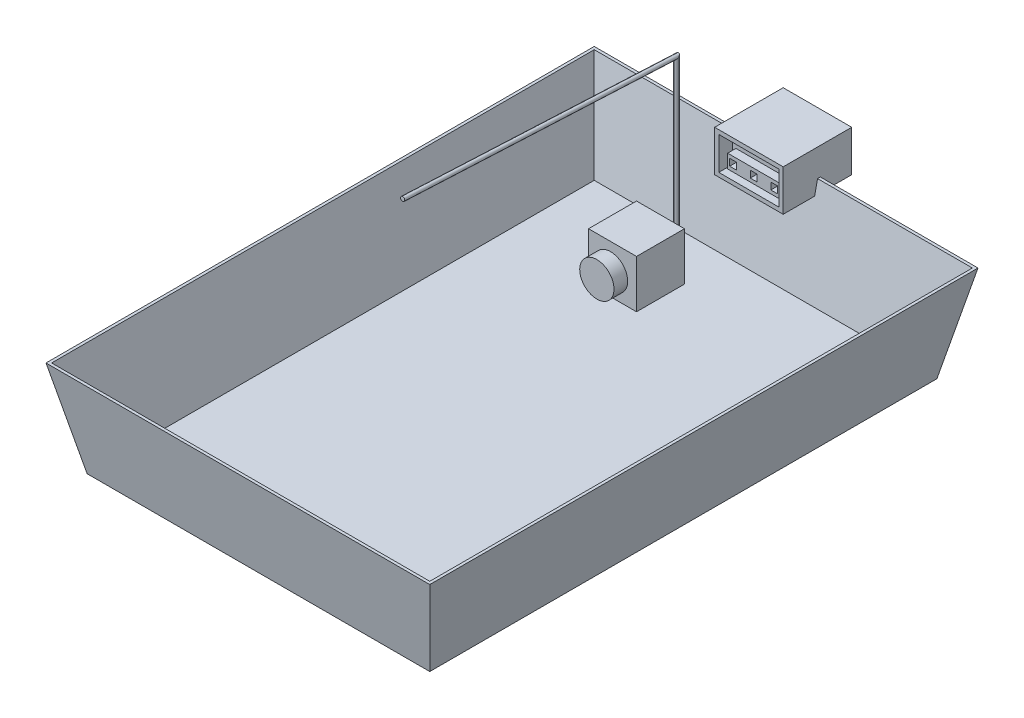
SolidWorks part; units mm, degrees
ref_plane "Front Plane" through (0, 0, 0) normal (0, 0, 1) x (1, 0, 0)
ref_plane "Top Plane" through (0, 0, 0) normal (0, 1, 0) x (1, 0, 0)
ref_plane "Right Plane" through (0, 0, 0) normal (1, 0, 0) x (0, 0, -1)
sketch "Sketch1" plane through (0, 0, 0) normal (0, 1, 0) x (1, 0, 0)
  line L1 (-140, 200) -> (140, 200)
  line L2 (-140, 200) -> (-140, -200)
  line L3 (-140, -200) -> (140, -200)
  line L4 (140, 200) -> (140, -200)
  line L5 (-140, 200) -> (140, -200) construction
  line L6 (-140, -200) -> (140, 200) construction
  point P0 (0, 0)
  dimension "D1" = 400
  dimension "D2" = 280
ref_plane "Plane1" through (0, -70, 0) normal (0, 1, 0) x (1, 0, 0)
sketch "Sketch2" plane through (0, -70, 0) normal (0, 1, 0) x (1, 0, 0)
  line L8 (125, 185) -> (-125, 185)
  line L9 (125, -185) -> (125, 185)
  line L10 (-125, -185) -> (125, -185)
  line L11 (-125, 185) -> (-125, -185)
  line L12 (125, 185) -> (-125, 185)
  line L13 (125, -185) -> (125, 185)
  line L14 (-125, -185) -> (125, -185)
  line L15 (-125, 185) -> (-125, -185)
  dimension "D1" = 15
loft "Loft1" add profiles "Sketch2", "Sketch1"
shell "Shell1" thickness 2
sketch "Sketch3" plane through (0, 0, 0) normal (0, 1, 0) x (1, 0, 0)
  line L0 (140, 200) -> (-140, 200) construction
  line L1 (-25, 225) -> (25, 225)
  line L2 (-25, 225) -> (-25, 175)
  line L3 (-25, 175) -> (25, 175)
  line L4 (25, 225) -> (25, 175)
  line L5 (-25, 225) -> (25, 175) construction
  line L6 (-25, 175) -> (25, 225) construction
  point P0 (0, 200)
  dimension "D1" = 50
extrude "Cut-Extrude1" cut sketch "Sketch3" against normal blind 10
sketch "Sketch4" plane through (0, -10, 0) normal (0, 1, 0) x (1, 0, 0)
  line L0 (25, 197.8571) -> (-25, 197.8571) construction
  line L1 (25, 172.8571) -> (-25, 172.8571)
  line L2 (25, 172.8571) -> (25, 222.8571)
  line L3 (25, 222.8571) -> (-25, 222.8571)
  line L4 (-25, 172.8571) -> (-25, 222.8571)
  line L5 (25, 172.8571) -> (-25, 222.8571) construction
  line L6 (25, 222.8571) -> (-25, 172.8571) construction
  point P0 (0, 197.8571)
  dimension "D1" = 50
extrude "Boss-Extrude2" add sketch "Sketch4" along normal blind 30 separate body
sketch "Sketch6" plane through (0, 0, -172.8571) normal (0, 0, 1) x (1, 0, 0)
  line L14 (-22, -7) -> (22, -7)
  line L15 (22, -7) -> (22, 17)
  line L16 (-22, 17) -> (-22, -7)
  line L17 (22, 17) -> (-22, 17)
  line L18 (-22, -7) -> (22, -7)
  line L19 (22, -7) -> (22, 17)
  line L20 (-22, 17) -> (-22, -7)
  line L21 (22, 17) -> (-22, 17)
  dimension "D1" = 3
extrude "Cut-Extrude2" cut sketch "Sketch6" against normal blind 10
sketch "Sketch7" plane through (0, 0, -222.8571) normal (0, 0, -1) x (-1, 0, 0)
  line L8 (-20, -5) -> (20, -5)
  line L9 (20, -5) -> (20, 15)
  line L10 (20, 15) -> (-20, 15)
  line L11 (-20, 15) -> (-20, -5)
  line L12 (-20, -5) -> (20, -5)
  line L13 (20, -5) -> (20, 15)
  line L14 (20, 15) -> (-20, 15)
  line L15 (-20, 15) -> (-20, -5)
  dimension "D1" = 5
extrude "Cut-Extrude3" cut sketch "Sketch7" against normal blind 10
sketch "Sketch8" plane through (0, 0, -182.8571) normal (0, 0, 1) x (1, 0, 0)
  circle A0 centre (-15.3016, 11.712) radius 2.5
  circle A1 centre (-7.1335, 11.712) radius 2.5
  dimension "D1" = 5
  dimension "D2" = 5
extrude "Cut-Extrude4" cut sketch "Sketch8" against normal blind 60
sketch "Sketch9" plane through (0, 0, -182.8571) normal (0, 0, 1) x (1, 0, 0)
  line L0 (-19.4953, 4.3816) -> (20.5047, 4.3816)
  line L1 (20.5047, 4.3816) -> (20.5047, -5.6184)
  line L2 (20.5047, -5.6184) -> (-19.4953, -5.6184)
  line L3 (-19.4953, -5.6184) -> (-19.4953, 4.3816)
  line L4 (1.9885, 1.8816) -> (1.9885, -3.1184)
  line L5 (-18.0115, 1.8816) -> (-13.0115, 1.8816)
  line L6 (-18.0115, 1.8816) -> (-18.0115, -3.1184)
  line L7 (-18.0115, -3.1184) -> (-13.0115, -3.1184)
  line L8 (-13.0115, 1.8816) -> (-13.0115, -3.1184)
  line L9 (-18.0115, 1.8816) -> (-13.0115, -3.1184) construction
  line L10 (-18.0115, -3.1184) -> (-13.0115, 1.8816) construction
  line L11 (-3.0115, -3.1184) -> (1.9885, -3.1184)
  line L12 (-3.0115, 1.8816) -> (-3.0115, -3.1184)
  line L13 (-3.0115, 1.8816) -> (1.9885, 1.8816)
  line L14 (16.9885, 1.8816) -> (16.9885, -3.1184)
  line L15 (11.9885, -3.1184) -> (16.9885, -3.1184)
  line L16 (11.9885, 1.8816) -> (11.9885, -3.1184)
  line L17 (11.9885, 1.8816) -> (16.9885, 1.8816)
  point P4 (-15.5115, -0.6184)
  dimension "D1" = 40
  dimension "D2" = 10
  dimension "D3" = 5
  dimension "D4" = 3
extrude "Boss-Extrude3" add sketch "Sketch9" along normal blind 6 contours L3 L2 L1 L0 L5 L8 L7 L6 L12 L13 L4 L11 L16 L17 L14 L15
sketch "Sketch10" plane through (0, -68, 0) normal (0, 1, 0) x (1, 0, 0)
  line L1 (-59.8965, 150.745) -> (-24.8965, 150.745)
  line L2 (-59.8965, 150.745) -> (-59.8965, 115.745)
  line L3 (-59.8965, 115.745) -> (-24.8965, 115.745)
  line L4 (-24.8965, 150.745) -> (-24.8965, 115.745)
  line L5 (-59.8965, 150.745) -> (-24.8965, 115.745) construction
  line L6 (-59.8965, 115.745) -> (-24.8965, 150.745) construction
  point P0 (-42.3965, 133.245)
  dimension "D1" = 35
extrude "Boss-Extrude5" add sketch "Sketch10" along normal blind 35 separate body
sketch "Sketch11" plane through (0, 0, -115.745) normal (0, 0, 1) x (1, 0, 0)
  line L0 (-24.8965, -33) -> (-59.8965, -68) construction
  circle A0 centre (-43.8438, -51.9473) radius 12.5
  dimension "D1" = 25
extrude "Boss-Extrude6" add sketch "Sketch11" along normal blind 10
ref_plane "Plane2" through (-34.8965, 0, 0) normal (-1, 0, 0) x (0, 0, 1)
sketch "Sketch12" plane through (-34.8965, 0, 0) normal (-1, 0, 0) x (0, 0, 1)
  line L0 (-149.8775, -51.005) -> (-154.8775, -51.005)
  line L1 (-154.8775, -51.005) -> (-154.8775, 68.995)
  line L2 (-154.8775, 68.995) -> (44.8898, 78.6393)
  dimension "D1" = 5
  dimension "D2" = 120
  dimension "D3" = 200
sweep "Sweep1" add path "Sketch12" circular profile diameter 3 parameters "D3"=3
